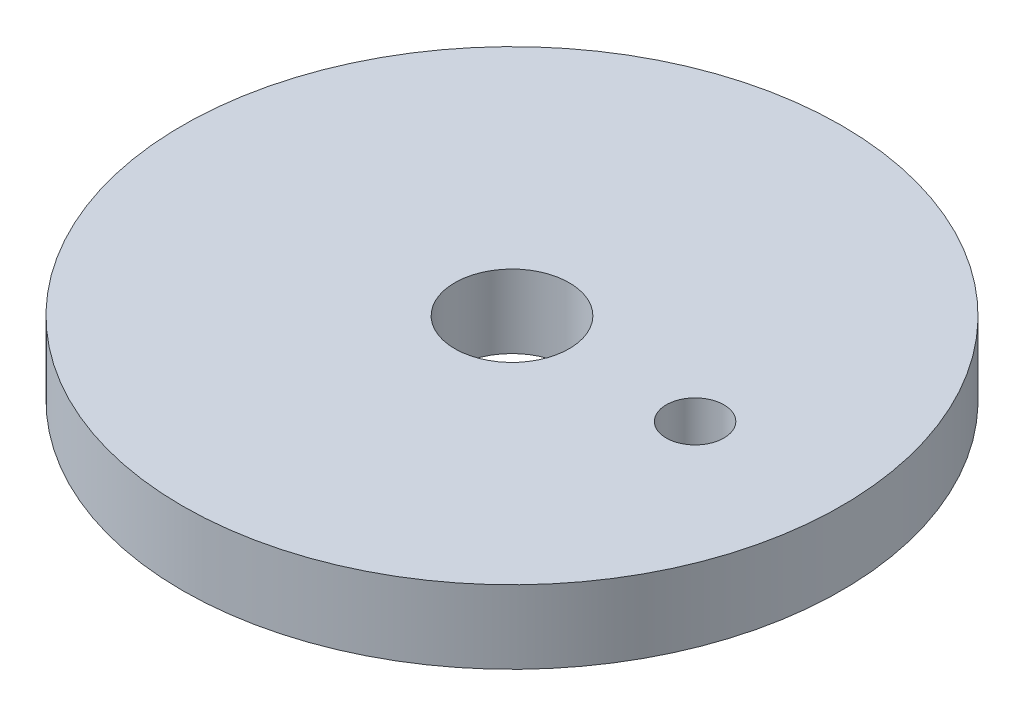
SolidWorks part; units mm, degrees
material "Delrin 2700 NC010, Low Viscosity Acetal Copolymer (SS)"
ref_plane "Front Plane" through (0, 0, 0) normal (0, 0, 1) x (1, 0, 0)
ref_plane "Top Plane" through (0, 0, 0) normal (0, 1, 0) x (1, 0, 0)
ref_plane "Right Plane" through (0, 0, 0) normal (1, 0, 0) x (0, 0, -1)
sketch "Sketch1" plane through (0, 0, 0) normal (0, 1, 0) x (1, 0, 0)
  line L0 (0, 0) -> (12.7, 0) construction
  circle A0 centre (0, 0) radius 22.86
  circle A1 centre (0, 0) radius 3.9688
  circle A2 centre (12.7, 0) radius 2
  dimension "D1" = 45.72
  dimension "D2" = 7.9375
  dimension "D3" = 4
  dimension "D4" = 12.7
extrude "Boss-Extrude1" add sketch "Sketch1" along normal blind 5.08
other "Move Face1" [suppressed] parameters "D1"=0.0508
